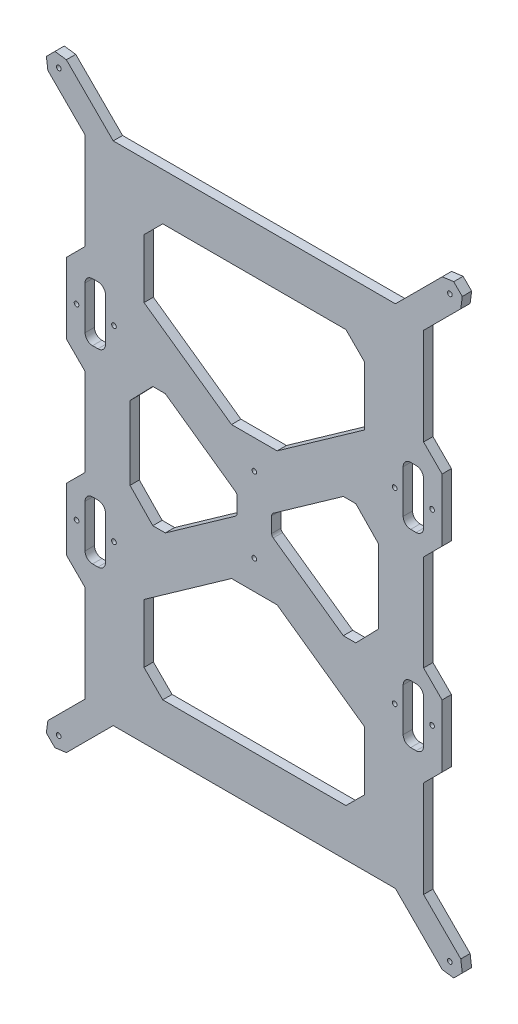
SolidWorks part; units mm, degrees
ref_plane "Piano frontale" through (0, 0, 0) normal (0, 0, 1) x (1, 0, 0)
ref_plane "Piano superiore" through (0, 0, 0) normal (0, 1, 0) x (1, 0, 0)
ref_plane "Piano destro" through (0, 0, 0) normal (1, 0, 0) x (0, 0, -1)
sketch "Schizzo1" plane through (0, 0, 0) normal (0, 0, 1) x (1, 0, 0)
  line L0 (-66.4357, 19.6293) -> (-66.4357, -19.6293)
  line L1 (-86.4486, 39.007) -> (-83.5514, 39.007) construction
  line L2 (-111.1309, 156.5575) -> (-106.5575, 161.1309)
  line L3 (-85, 39.007) -> (-85, 72.1548) construction
  line L4 (-111.1309, 156.5575) -> (-110.3308, 150.4313)
  line L5 (-110.3308, 150.4313) -> (-90.4486, 130.5491)
  line L6 (-90.4486, 130.5491) -> (-90.4486, 78.8741)
  line L7 (-90.4486, 78.8741) -> (-100.3308, 68.992)
  line L8 (-90.4486, 21.1259) -> (-90.4486, -25.6817)
  line L9 (-9.2567, 4.0961) -> (-9.2567, -4.0961)
  line L10 (0, 0) -> (-165.9293, 0) construction
  line L11 (-58.9422, 100.14) -> (-58.9422, 68.7002)
  line L12 (-58.9422, 100.14) -> (-48.9422, 110.14)
  line L13 (-86.4486, 35.007) -> (-83.5514, 35.007)
  line L14 (-75, 50) -> (-107.9533, 50) construction
  line L15 (-79.5514, 39.007) -> (-79.5514, 62.007)
  line L16 (-104.5, 154.5) -> (0, 50) construction
  line L17 (-106.5575, 161.1309) -> (-100.4313, 160.3308)
  line L18 (75, 50) -> (107.9533, 50) construction
  line L19 (85, 39.007) -> (85, 72.1548) construction
  line L20 (86.4486, 39.007) -> (83.5514, 39.007) construction
  line L21 (86.4486, 66.007) -> (83.5514, 66.007)
  line L22 (0, 0) -> (0, 265.525) construction
  line L23 (90.4486, 39.007) -> (90.4486, 62.007)
  line L24 (-100.3308, 68.992) -> (-100.3308, 31.008)
  line L25 (-90.4486, 21.1259) -> (-100.3308, 31.008)
  line L26 (100.4313, 160.3308) -> (75.3933, 135.2928)
  line L27 (47.5638, 32.2218) -> (10.1019, 5.729)
  line L28 (54.2431, 32.2218) -> (47.5638, 32.2218)
  line L29 (-58.9422, 68.7002) -> (-12.1818, 35.6316)
  line L30 (-12.1818, 35.6316) -> (12.1818, 35.6316)
  line L31 (66.4357, 19.6293) -> (54.2431, 32.2218)
  line L32 (58.9422, 68.7002) -> (12.1818, 35.6316)
  line L33 (-75.3933, 135.2928) -> (75.3933, 135.2928)
  line L34 (90.4486, 25.6817) -> (100.3308, 35.5638)
  line L35 (100.3308, 68.992) -> (100.3308, 35.5638)
  line L36 (106.5575, 161.1309) -> (100.4313, 160.3308)
  line L37 (79.5514, 39.007) -> (79.5514, 62.007)
  line L38 (-66.4357, 19.6293) -> (-54.2431, 32.2218)
  line L39 (-54.2431, 32.2218) -> (-47.5638, 32.2218)
  line L40 (-47.5638, 32.2218) -> (-10.1019, 5.729)
  line L41 (86.4486, 35.007) -> (83.5514, 35.007)
  line L42 (58.9422, 100.14) -> (48.9422, 110.14)
  line L43 (58.9422, 100.14) -> (58.9422, 68.7002)
  line L44 (9.2567, 4.0961) -> (9.2567, -4.0961)
  line L45 (90.4486, 25.6817) -> (90.4486, -25.6817)
  line L46 (90.4486, 78.8741) -> (100.3308, 68.992)
  line L47 (90.4486, 130.5491) -> (90.4486, 78.8741)
  line L48 (110.3308, 150.4313) -> (90.4486, 130.5491)
  line L49 (111.1309, 156.5575) -> (110.3308, 150.4313)
  line L50 (111.1309, 156.5575) -> (106.5575, 161.1309)
  line L51 (66.4357, 19.6293) -> (66.4357, -19.6293)
  line L52 (-48.9422, 110.14) -> (48.9422, 110.14)
  line L53 (86.4486, -39.007) -> (83.5514, -39.007) construction
  line L54 (85, -39.007) -> (85, -72.1548) construction
  line L55 (75, -50) -> (107.9533, -50) construction
  line L56 (-75, -50) -> (-107.9533, -50) construction
  line L57 (-85, -39.007) -> (-85, -72.1548) construction
  line L58 (-86.4486, -39.007) -> (-83.5514, -39.007) construction
  line L59 (-86.4486, -66.007) -> (-83.5514, -66.007)
  line L60 (-90.4486, -39.007) -> (-90.4486, -62.007)
  line L61 (-100.4313, -160.3308) -> (-75.3933, -135.2928)
  line L62 (-48.9422, -110.14) -> (48.9422, -110.14)
  line L63 (-100.4313, 160.3308) -> (-75.3933, 135.2928)
  line L64 (111.1309, -156.5575) -> (106.5575, -161.1309)
  line L65 (111.1309, -156.5575) -> (110.3308, -150.4313)
  line L66 (110.3308, -150.4313) -> (90.4486, -130.5491)
  line L67 (90.4486, -130.5491) -> (90.4486, -78.8741)
  line L68 (90.4486, -78.8741) -> (100.3308, -68.992)
  line L69 (58.9422, -100.14) -> (58.9422, -68.7002)
  line L70 (58.9422, -100.14) -> (48.9422, -110.14)
  line L71 (86.4486, -35.007) -> (83.5514, -35.007)
  line L72 (-47.5638, -32.2218) -> (-10.1019, -5.729)
  line L73 (-54.2431, -32.2218) -> (-47.5638, -32.2218)
  line L74 (-90.4486, 39.007) -> (-90.4486, 62.007)
  line L75 (-86.4486, 66.007) -> (-83.5514, 66.007)
  line L76 (-66.4357, -19.6293) -> (-54.2431, -32.2218)
  line L77 (79.5514, -39.007) -> (79.5514, -62.007)
  line L78 (106.5575, -161.1309) -> (100.4313, -160.3308)
  line L79 (100.3308, -68.992) -> (100.3308, -35.5638)
  line L80 (90.4486, -25.6817) -> (100.3308, -35.5638)
  line L81 (-75.3933, -135.2928) -> (75.3933, -135.2928)
  line L82 (58.9422, -68.7002) -> (12.1818, -35.6316)
  line L83 (66.4357, -19.6293) -> (54.2431, -32.2218)
  line L84 (-12.1818, -35.6316) -> (12.1818, -35.6316)
  line L85 (-58.9422, -68.7002) -> (-12.1818, -35.6316)
  line L86 (54.2431, -32.2218) -> (47.5638, -32.2218)
  line L87 (47.5638, -32.2218) -> (10.1019, -5.729)
  line L88 (100.4313, -160.3308) -> (75.3933, -135.2928)
  line L89 (-90.4486, -25.6817) -> (-100.3308, -35.5638)
  line L90 (-100.3308, -68.992) -> (-100.3308, -35.5638)
  line L91 (90.4486, -39.007) -> (90.4486, -62.007)
  line L92 (86.4486, -66.007) -> (83.5514, -66.007)
  line L93 (-106.5575, -161.1309) -> (-100.4313, -160.3308)
  line L94 (-79.5514, -39.007) -> (-79.5514, -62.007)
  line L95 (-86.4486, -35.007) -> (-83.5514, -35.007)
  line L96 (-58.9422, -100.14) -> (-48.9422, -110.14)
  line L97 (-58.9422, -100.14) -> (-58.9422, -68.7002)
  line L98 (-90.4486, -78.8741) -> (-100.3308, -68.992)
  line L99 (-90.4486, -130.5491) -> (-90.4486, -78.8741)
  line L100 (-110.3308, -150.4313) -> (-90.4486, -130.5491)
  line L101 (-111.1309, -156.5575) -> (-110.3308, -150.4313)
  line L102 (-111.1309, -156.5575) -> (-106.5575, -161.1309)
  circle A0 centre (-95, 50) radius 1.25
  circle A1 centre (-75, 50) radius 1.25
  arc A2 (-79.5514, 39.007) -> (-83.5514, 35.007) centre (-83.5514, 39.007) cw
  arc A3 (-83.5514, 66.007) -> (-79.5514, 62.007) centre (-83.5514, 62.007) cw
  arc A4 (9.2567, 4.0961) -> (10.1019, 5.729) centre (11.2567, 4.0961) cw
  arc A5 (90.4486, 39.007) -> (86.4486, 35.007) centre (86.4486, 39.007) cw
  circle A6 centre (-104.5, 154.5) radius 1.25
  arc A7 (86.4486, 66.007) -> (90.4486, 62.007) centre (86.4486, 62.007) cw
  circle A8 centre (104.5, 154.5) radius 1.25
  arc A9 (83.5514, 66.007) -> (79.5514, 62.007) centre (83.5514, 62.007) ccw
  arc A10 (79.5514, 39.007) -> (83.5514, 35.007) centre (83.5514, 39.007) ccw
  circle A11 centre (75, 50) radius 1.25
  circle A12 centre (95, 50) radius 1.25
  arc A13 (-9.2567, -4.0961) -> (-10.1019, -5.729) centre (-11.2567, -4.0961) cw
  arc A14 (-90.4486, -39.007) -> (-86.4486, -35.007) centre (-86.4486, -39.007) cw
  circle A15 centre (0, 20.1313) radius 1.25
  arc A16 (-86.4486, -66.007) -> (-90.4486, -62.007) centre (-86.4486, -62.007) cw
  arc A17 (-86.4486, 66.007) -> (-90.4486, 62.007) centre (-86.4486, 62.007) ccw
  circle A18 centre (0, -20.1313) radius 1.25
  arc A19 (-90.4486, 39.007) -> (-86.4486, 35.007) centre (-86.4486, 39.007) ccw
  circle A20 centre (95, -50) radius 1.25
  circle A21 centre (75, -50) radius 1.25
  arc A22 (79.5514, -39.007) -> (83.5514, -35.007) centre (83.5514, -39.007) cw
  arc A23 (83.5514, -66.007) -> (79.5514, -62.007) centre (83.5514, -62.007) cw
  circle A24 centre (104.5, -154.5) radius 1.25
  arc A25 (86.4486, -66.007) -> (90.4486, -62.007) centre (86.4486, -62.007) ccw
  circle A26 centre (-104.5, -154.5) radius 1.25
  arc A27 (90.4486, -39.007) -> (86.4486, -35.007) centre (86.4486, -39.007) ccw
  arc A28 (9.2567, -4.0961) -> (10.1019, -5.729) centre (11.2567, -4.0961) ccw
  arc A29 (-83.5514, -66.007) -> (-79.5514, -62.007) centre (-83.5514, -62.007) ccw
  arc A30 (-9.2567, 4.0961) -> (-10.1019, 5.729) centre (-11.2567, 4.0961) ccw
  arc A31 (-79.5514, -39.007) -> (-83.5514, -35.007) centre (-83.5514, -39.007) ccw
  circle A32 centre (-75, -50) radius 1.25
  circle A33 centre (-95, -50) radius 1.25
  point P1 (-58.9422, -110.14)
  point P10 (-90.4486, 0)
  point P14 (-85, 35.007)
  point P22 (-85, 66.007)
  point P26 (-108.8442, 158.8442)
  point P66 (-66.4357, 0)
  point P69 (0, 110.14)
  point P72 (-100.3308, 50)
  point P77 (0, 135.2928)
  point P78 (0, 35.6316)
  point P88 (9.2567, 0)
  point P94 (58.9422, 110.14)
  point P96 (108.8442, 158.8442)
  point P97 (85, 66.007)
  point P98 (85, 35.007)
  point P133 (-58.9422, 110.14)
  point P167 (66.4357, 0)
  point P174 (90.4486, 0)
  point P194 (-9.2567, 0)
  point P198 (-66.4357, 0)
  point P199 (85, -35.007)
  point P200 (85, -66.007)
  point P201 (108.8442, -158.8442)
  point P203 (58.9422, -110.14)
  point P204 (0, -35.6316)
  point P205 (0, -135.2928)
  point P207 (0, -110.14)
  point P208 (-108.8442, -158.8442)
  point P209 (-85, -66.007)
  point P210 (-85, -35.007)
  dimension "D1" = 154.5
  dimension "D2" = 104.5
  dimension "D3" = 20
  dimension "D5" = 2
  dimension "D6" = 85
  dimension "D11" = 2.5
  dimension "D7" = 23
  dimension "D8" = 45
  dimension "D9" = 14
  dimension "D10" = 50
extrude "Estrusione-Estrusione1" add sketch "Schizzo1" against normal blind 5
sketch "Schizzo2" [suppressed] plane through (0, 0, 0) normal (0, 0, 1) x (1, 0, 0)
  line L0 (0, 0) -> (0, 148.2594) construction
  line L1 (58.9422, 84.4201) -> (-108.2298, 84.4201) construction
  line L2 (58.9422, 68.7002) -> (58.9422, 100.14) construction
  line L3 (0, 0) -> (-115.6703, 0) construction
  point P0 (29.4418, 84.4201)
  point P8 (-29.4418, 84.4201)
  point P10 (-55.8026, 0)
  point P12 (-29.4418, 0)
  point P13 (55.8026, 0)
  point P14 (29.4418, 0)
  point P15 (29.4418, -84.4201)
  point P16 (-29.4418, -84.4201)
